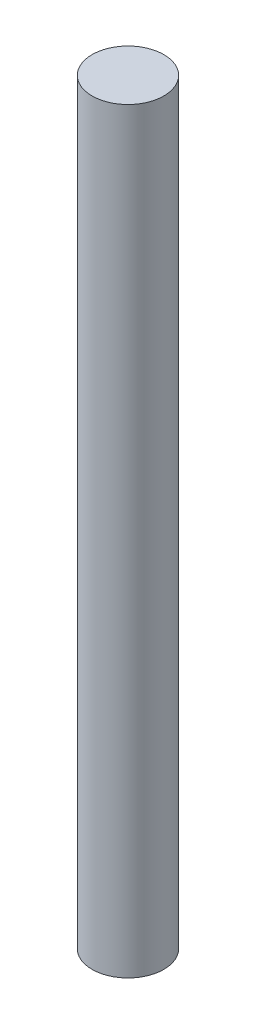
SolidWorks part; units mm, degrees
material "EFI Alloy 79"
ref_plane "Front Plane" through (0, 0, 0) normal (0, 0, 1) x (1, 0, 0)
ref_plane "Top Plane" through (0, 0, 0) normal (0, 1, 0) x (1, 0, 0)
ref_plane "Right Plane" through (0, 0, 0) normal (1, 0, 0) x (0, 0, -1)
sketch "Sketch1" plane through (0, 0, 0) normal (0, 1, 0) x (1, 0, 0)
  circle A0 centre (0, 0) radius 3.3655
extrude "Boss-Extrude1" add sketch "Sketch1" along normal blind 71
